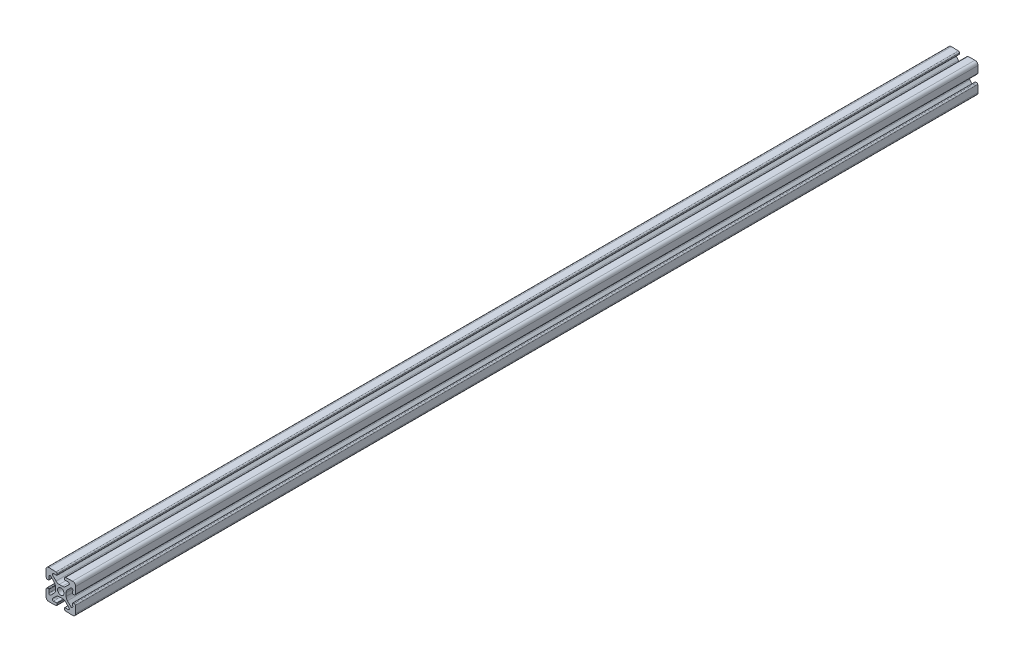
SolidWorks part; units mm, degrees
ref_plane "Front Plane" through (0, 0, 0) normal (0, 0, 1) x (1, 0, 0)
ref_plane "Top Plane" through (0, 0, 0) normal (0, 1, 0) x (1, 0, 0)
ref_plane "Right Plane" through (0, 0, 0) normal (1, 0, 0) x (0, 0, -1)
sketch "Sketch1" plane through (0, 0, 0) normal (0, 0, 1) x (1, 0, 0)
  line L0 (0, 0) -> (0, 10) construction
  line L1 (0, 0) -> (10, 0) construction
  line L2 (0, 0) -> (-10, 10) construction
  line L3 (-7.9302, 9.9988) -> (-3.2721, 9.8361)
  line L4 (-10, 10) -> (0, 10) construction
  line L6 (-2.8352, 8.0198) -> (-4.953, 8.0937)
  line L10 (0, 3.6) -> (-1.1022, 3.6)
  line L11 (-3.2236, 4.4787) -> (-5.5244, 6.7796)
  line L24 (0, 0) -> (-10, 0) construction
  line L25 (-10, 0) -> (0, 0) construction
  line L26 (0, 0) -> (0, -10) construction
  line L27 (-10, -10) -> (-10, 10) construction
  line L28 (0, 10) -> (10, 10) construction
  line L29 (-2.5249, 8.3091) -> (-2.5005, 9.0087)
  line L30 (-10, -10) -> (10, -10) construction
  arc A0 (-9.4142, 9.4142) -> (-7.9302, 9.9988) centre (-8, 8) cw
  arc A5 (-3.2721, 9.8361) -> (-2.5005, 9.0087) centre (-3.3, 9.0366) cw
  arc A6 (-1.1022, 3.6) -> (-3.2236, 4.4787) centre (-1.1022, 6.6) cw
  circle A16 centre (0, 0) radius 2.15
  arc A18 (-5.5244, 6.7796) -> (-4.953, 8.0937) centre (-4.9799, 7.3241) cw
  arc A20 (-2.8352, 8.0198) -> (-2.5249, 8.3091) centre (-2.8247, 8.3196) ccw
  point P15 (0, 0)
  point P42 (-2.3449, 3.6)
  point P80 (-10, 0)
  point P85 (0, -10)
  point P88 (0, -10)
  dimension "D11" = 2
  dimension "D15" = 3
  dimension "Center Hole Diameter" = 4.3
  dimension "D7" = 0.8
  dimension "D8" = 0.3
  dimension "D4" = 0.7701
  dimension "D1" = 45
  dimension "D2" = 2
  dimension "Rail Width" = 20
  dimension "T-Slot Depth" = 6.4
  dimension "D9" = 1.8
  dimension "Rail Height" = 20
  dimension "D23" = 7.2
  dimension "D5" = 11.5
  dimension "T-Slot Width" = 5
  dimension "D3" = 1.775
  dimension "D6" = 9.9598
sketch "Sketch2" plane through (0, 0, 0) normal (1, 0, 0) x (0, 0, -1)
  line L0 (-304.8, 0) -> (304.8, 0)
  line L1 (-304.8, -10) -> (-304.8, 10)
  line L2 (0, 0) -> (0, 10) construction
  line L3 (0, 0) -> (0, 10) construction
  line L4 (304.8, -10) -> (304.8, 10)
  point P0 (-274.8, 0)
  point P3 (0, 0)
  point P7 (274.8, 0)
  point P11 (-304.8, 0)
  point P14 (304.8, 0)
  dimension "D1" = 30
  dimension "Length" = 609.6
sketch "Sketch3" plane through (0, 0, 0) normal (0, 0, 1) x (1, 0, 0)
  line L0 (-2.5249, 8.3091) -> (-2.5005, 9.0087) construction
  line L1 (0, 0) -> (-10, 10) construction
  line L2 (0, 0) -> (-10, 10) construction
  line L5 (-7.9302, 9.9988) -> (-3.2721, 9.8361) construction
  line L6 (-2.8352, 8.0198) -> (-4.953, 8.0937) construction
  line L17 (-2.5249, 8.3091) -> (-2.5005, 9.0087)
  line L19 (-2.8352, 8.0198) -> (-4.953, 8.0937)
  line L20 (0, 0) -> (0, 10) construction
  line L21 (-3.6, 0) -> (-2.15, 0)
  line L22 (-3.6, 0) -> (-3.6, 1.1022)
  line L23 (-4.4787, 3.2236) -> (-6.7796, 5.5244)
  line L42 (-3.2236, 4.4787) -> (-5.5244, 6.7796) construction
  line L43 (0, 3.6) -> (-1.1022, 3.6) construction
  line L44 (-7.9302, 9.9988) -> (-3.2721, 9.8361)
  line L47 (-3.2236, 4.4787) -> (-5.5244, 6.7796)
  line L48 (0, 3.6) -> (-1.1022, 3.6)
  line L59 (0, 3.6) -> (0, 2.15)
  line L60 (-9.9988, 7.9302) -> (-9.8361, 3.2721)
  line L61 (-8.0198, 2.8352) -> (-8.0937, 4.953)
  line L62 (-8.3091, 2.5249) -> (-9.0087, 2.5005)
  arc A0 (-7.9302, 9.9988) -> (-9.4142, 9.4142) centre (-8, 8) ccw construction
  arc A1 (-2.8352, 8.0198) -> (-2.5249, 8.3091) centre (-2.8247, 8.3196) ccw construction
  arc A3 (-2.8352, 8.0198) -> (-2.5249, 8.3091) centre (-2.8247, 8.3196) ccw
  arc A5 (-7.9302, 9.9988) -> (-9.9988, 7.9302) centre (-8, 8) ccw
  circle A13 centre (0, 0) radius 2.15 construction
  arc A14 (0, 2.15) -> (-2.15, 0) centre (0, 0) ccw
  arc A15 (-4.4787, 3.2236) -> (-3.6, 1.1022) centre (-6.6, 1.1022) cw
  arc A16 (-8.0937, 4.953) -> (-6.7796, 5.5244) centre (-7.3241, 4.9799) cw
  arc A17 (-9.0087, 2.5005) -> (-9.8361, 3.2721) centre (-9.0366, 3.3) cw
  arc A18 (-8.0198, 2.8352) -> (-8.3091, 2.5249) centre (-8.3196, 2.8247) cw
  arc A36 (-2.5005, 9.0087) -> (-3.2721, 9.8361) centre (-3.3, 9.0366) ccw construction
  arc A38 (-4.953, 8.0937) -> (-5.5244, 6.7796) centre (-4.9799, 7.3241) ccw construction
  arc A39 (-3.2236, 4.4787) -> (-1.1022, 3.6) centre (-1.1022, 6.6) ccw construction
  arc A41 (-2.5005, 9.0087) -> (-3.2721, 9.8361) centre (-3.3, 9.0366) ccw
  arc A43 (-4.953, 8.0937) -> (-5.5244, 6.7796) centre (-4.9799, 7.3241) ccw
  arc A44 (-3.2236, 4.4787) -> (-1.1022, 3.6) centre (-1.1022, 6.6) ccw
extrude "Boss-Extrude1" add sketch "Sketch3" along normal mid plane 609.6
pattern_circular "CirPattern1" count 4 over 360 about axis through (0, 0, 0) along (0, 0, 1) of "Boss-Extrude1"
ref_plane "Contact Plane 1" through (0, 10, 0) normal (0, 1, 0) x (1, 0, 0)
ref_plane "Contact Plane 2" through (10, 0, 0) normal (1, 0, 0) x (0, 0, -1)
ref_plane "Contact Plane 3" through (0, -10, 0) normal (0, -1, 0) x (-1, 0, 0)
ref_plane "Contact Plane 4" through (-10, 0, 0) normal (-1, 0, 0) x (0, 0, 1)
equation "\"D1@Sketch2\"=\"Rail Width@Sketch1\"*1.5"
equation "\"D1@Boss-Extrude1\" = \"Length@Sketch2\""
